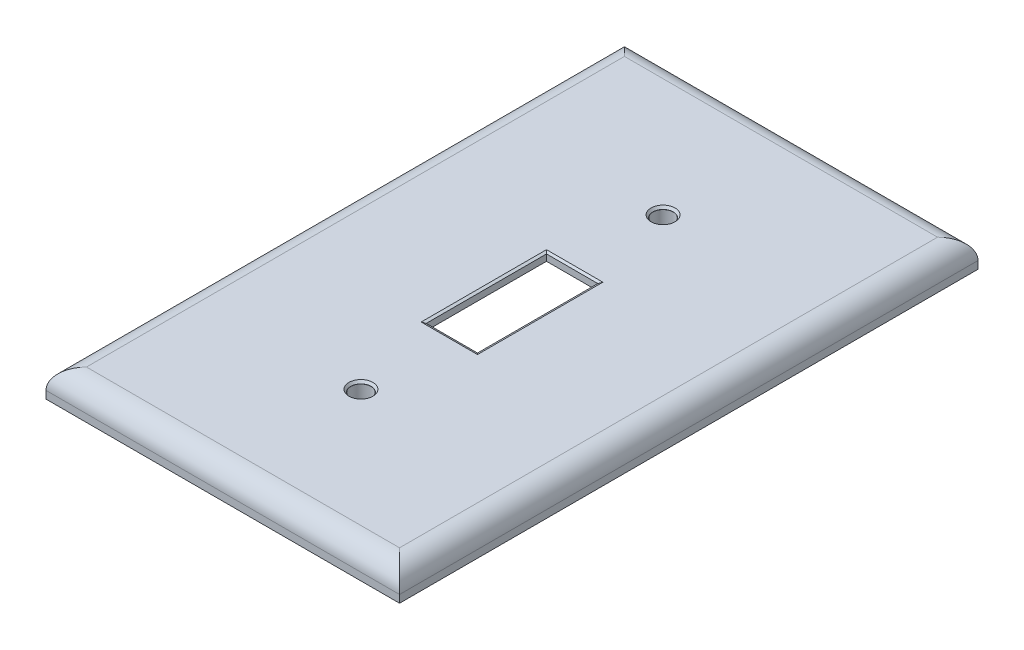
SolidWorks part; units mm, degrees
ref_plane "Front Plane" through (0, 0, 0) normal (0, 0, 1) x (1, 0, 0)
ref_plane "Top Plane" through (0, 0, 0) normal (0, 1, 0) x (1, 0, 0)
ref_plane "Right Plane" through (0, 0, 0) normal (1, 0, 0) x (0, 0, -1)
sketch "Sketch1" plane through (0, 0, 0) normal (0, 1, 0) x (1, 0, 0)
  line L1 (-34.97, -57.215) -> (34.97, -57.215)
  line L2 (-34.97, -57.215) -> (-34.97, 57.215)
  line L3 (-34.97, 57.215) -> (34.97, 57.215)
  line L4 (34.97, -57.215) -> (34.97, 57.215)
  line L5 (-34.97, -57.215) -> (34.97, 57.215) construction
  line L6 (-34.97, 57.215) -> (34.97, -57.215) construction
  point P0 (0, 0)
  dimension "D1" = 69.94
  dimension "D2" = 114.43
extrude "Boss-Extrude1" add sketch "Sketch1" along normal blind 5.5
fillet "Fillet1" radius 4 4 edges at (0, 5.5, 57.215) (-34.97, 5.5, 0) (0, 5.5, -57.215) (34.97, 5.5, 0)
ref_plane "Plane1" through (0, -2, 0) normal (0, 1, 0) x (1, 0, 0)
sketch "Sketch5" plane through (0, -2, 0) normal (0, 1, 0) x (1, 0, 0)
  line L1 (-33.785, -56.03) -> (33.785, -56.03)
  line L2 (-33.785, -56.03) -> (-33.785, 56.03)
  line L3 (-33.785, 56.03) -> (33.785, 56.03)
  line L4 (33.785, -56.03) -> (33.785, 56.03)
  line L5 (-33.785, -56.03) -> (33.785, 56.03) construction
  line L6 (-33.785, 56.03) -> (33.785, -56.03) construction
  point P0 (0, 0)
  dimension "D1" = 112.06
  dimension "D2" = 67.57
extrude "Cut-Extrude1" cut sketch "Sketch5" along normal blind 6
fillet "Fillet4" radius 2.5 4 edges at (0, 4, -56.03) (-33.785, 4, 0) (0, 4, 56.03) (33.785, 4, 0)
ref_plane "Plane2" through (0, 4, 0) normal (0, -1, 0) x (-1, 0, 0)
ref_plane "Plane3" through (0, 0, -59.215) normal (0, 0, -1) x (-1, 0, 0)
sketch "Sketch12" plane through (0, 0, -59.215) normal (0, 0, -1) x (-1, 0, 0)
  line L0 (-31.285, 4) -> (31.285, 4) construction
  line L1 (21.6852, 4) -> (17.8153, 4)
  line L2 (0, 0) -> (0, 15.1004) construction
  line L4 (-21.6852, 4) -> (-17.8153, 4)
  arc A0 (21.6852, 4) -> (17.8153, 4) centre (19.7503, 4.5059) cw
  arc A1 (-21.6852, 4) -> (-17.8153, 4) centre (-19.7503, 4.5059) ccw
extrude "Boss-Extrude8" add sketch "Sketch12" against normal blind 112.5 from offset 3 offset against normal yes
ref_plane "Plane5" through (33.97, 0, 0) normal (1, 0, 0) x (0, 0, -1)
sketch "Sketch15" plane through (33.97, 0, 0) normal (1, 0, 0) x (0, 0, -1)
  line L0 (0, 16.3374) -> (0, -9.5803) construction
  line L4 (-29.885, 9.2717) -> (-29.885, -2.7261) construction
  line L6 (-31.885, 3.965) -> (-27.885, 3.965)
  line L7 (31.885, 3.965) -> (27.885, 3.965)
  arc A0 (31.885, 3.965) -> (27.885, 3.965) centre (29.885, 3.965) cw
  arc A1 (-31.885, 3.965) -> (-27.885, 3.965) centre (-29.885, 3.965) ccw
  point P5 (-29.885, 4.75)
extrude "Boss-Extrude10" add sketch "Sketch15" against normal blind 68
sketch "Sketch17" plane through (0, 4, 0) normal (0, -1, 0) x (-1, 0, 0)
  line L0 (38.107, 0) -> (-45.2944, 0) construction
  circle A0 centre (0, -29.885) radius 2.5
  circle A1 centre (0, 29.885) radius 2.5
  dimension "D1" = 5
extrude "Boss-Extrude11" add sketch "Sketch17" along normal blind 4
sketch "Sketch13" plane through (0, 0, 0) normal (0, 1, 0) x (1, 0, 0)
  line L0 (-38.6421, 0) -> (0, 0) construction
  line L1 (0, 0) -> (42.6549, 0) construction
  line L2 (0, 59.8209) -> (0, 0) construction
  line L3 (0, 0) -> (0, -62.4961) construction
  line L4 (-34.97, 57.215) -> (34.97, 57.215) construction
  line L6 (5.075, -11.9) -> (-5.075, -11.9)
  line L7 (5.075, -11.9) -> (5.075, 11.9)
  line L8 (5.075, 11.9) -> (-5.075, 11.9)
  line L9 (-5.075, -11.9) -> (-5.075, 11.9)
  line L10 (5.075, -11.9) -> (-5.075, 11.9) construction
  line L11 (5.075, 11.9) -> (-5.075, -11.9) construction
  circle A0 centre (0, 29.885) radius 1.99
  circle A1 centre (0, -29.885) radius 1.99
  dimension "D1" = 3.98
  dimension "D2" = 27.33
  dimension "D3" = 23.8
  dimension "D4" = 10.15
extrude "Cut-Extrude2" cut sketch "Sketch13" along normal blind 10
ref_plane "Plane6" through (0, 6.5, 0) normal (0, 1, 0) x (1, 0, 0)
sketch "Sketch16" plane through (0, 6.5, 0) normal (0, 1, 0) x (1, 0, 0)
  line L0 (-38.6223, 0) -> (45.0086, 0) construction
  line L1 (0, 61.3547) -> (0, -64.5478) construction
  line L2 (0, 29.885) -> (45.0086, 29.885) construction
  line L3 (0, 29.885) -> (-42.6466, 29.885) construction
  circle A0 centre (0, 29.885) radius 3.075
  circle A1 centre (0, -29.885) radius 3.075
  dimension "D1" = 6.15
extrude "Cut-Extrude3" cut sketch "Sketch16" against normal blind 1.5 draft 35
chamfer "Chamfer1" distance 0.5 angle 25 4 edges at (5.075, 5.5, 0) (0, 5.5, 11.9) (-5.075, 5.5, 0) (0, 5.5, -11.9)
